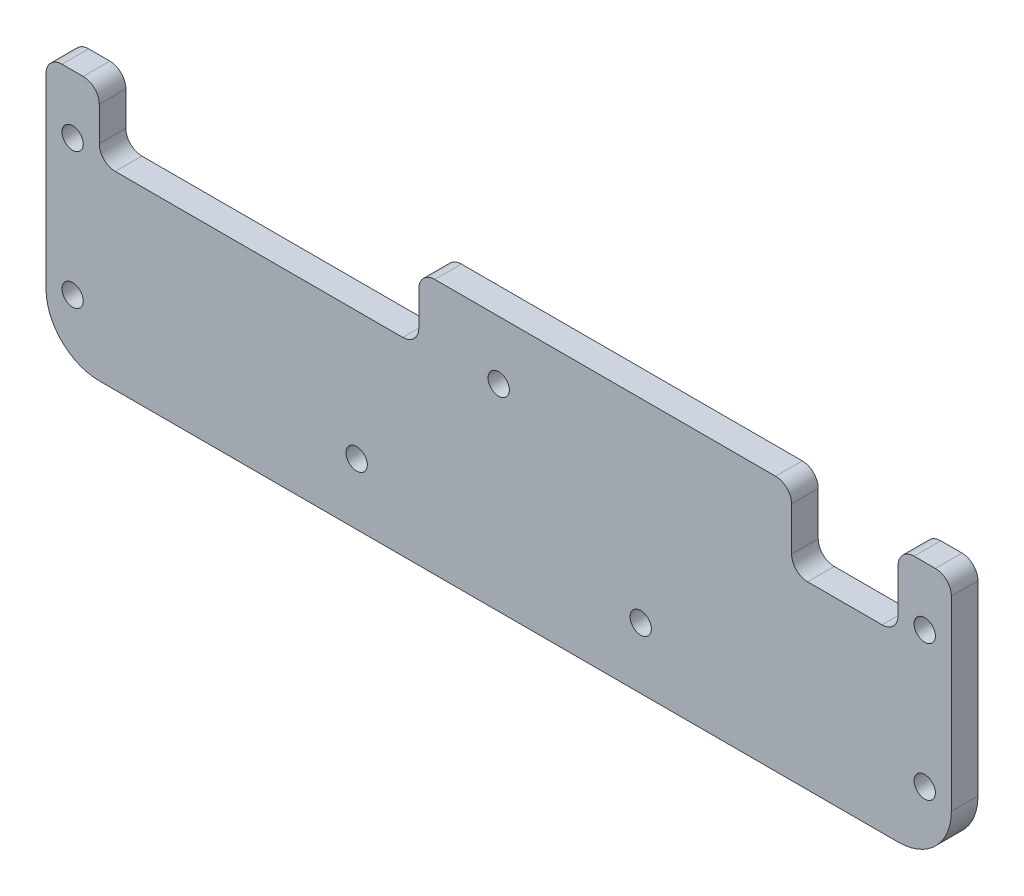
SolidWorks part; units mm, degrees
material "Thornel Mat VMA"
ref_plane "前视基准面" through (0, 0, 0) normal (0, 0, 1) x (1, 0, 0)
ref_plane "上视基准面" through (0, 0, 0) normal (0, 1, 0) x (1, 0, 0)
ref_plane "右视基准面" through (0, 0, 0) normal (1, 0, 0) x (0, 0, -1)
sketch "草图1" plane through (0, 0, 0) normal (0, 0, 1) x (1, 0, 0)
  line L0 (-85, 0) -> (85, 0)
  line L1 (-85, 0) -> (-85, -38)
  line L2 (-75, -48) -> (75, -48)
  line L3 (0, -2.75) -> (0, 2.75) construction
  line L4 (85, 0) -> (85, -38)
  arc A0 (-75, -48) -> (-85, -38) centre (-75, -38) cw
  circle A2 centre (-80, -11) radius 2
  circle A3 centre (0, -11) radius 2
  circle A4 centre (80, -11) radius 2
  circle A5 centre (-80, -36.5) radius 2
  circle A9 centre (80, -36.5) radius 2
  arc A10 (85, -38) -> (75, -48) centre (75, -38) cw
  circle A11 centre (-26.6667, -36.5) radius 2
  circle A12 centre (26.6667, -36.5) radius 2
  point P12 (0, -48)
  point P13 (0, 0)
  dimension "D3" = 10
  dimension "D7" = 4
  dimension "D8" = 4
  dimension "D9" = 4
  dimension "D10" = 36.5
  dimension "D15" = 10
  dimension "D12" = 4
  dimension "D17" = 4
  dimension "D19" = 4
  dimension "D1" = 85
  dimension "D2" = 48
  dimension "D4" = 80
  dimension "D5" = 80
  dimension "D6" = 11
  dimension "D13" = 5
  dimension "D14" = 5
  dimension "D16" = 5
  dimension "D20" = 26.6667
extrude "凸台-拉伸1" add sketch "草图1" along normal blind 5
sketch "草图2" plane through (0, 0, 0) normal (0, 0, 1) x (1, 0, 0)
  line L0 (-85, 0) -> (-85, -38) construction
  line L1 (-15, 12.1435) -> (-75, 12.1435)
  line L2 (-15, 12.1435) -> (-15, -12.4346)
  line L3 (-15, -12.4346) -> (-75, -12.4346)
  line L4 (-75, 12.1435) -> (-75, -12.4346)
  line L5 (75, 4.04) -> (55, 4.04)
  line L6 (75, 4.04) -> (75, -14.1694)
  line L7 (75, -14.1694) -> (55, -14.1694)
  line L8 (55, 4.04) -> (55, -14.1694)
  line L9 (85, -38) -> (85, 0) construction
  dimension "D1" = 10
  dimension "D2" = 20
  dimension "D3" = 10
  dimension "D4" = 60
extrude "切除-拉伸1" cut sketch "草图2" along normal blind 29
fillet "圆角1" radius 3 10 edges at (85, 0, 2.5) (-85, 0, 2.5) (-75, 0, 2.5) (-75, -12.4346, 2.5) (-15, -12.4346, 2.5) (-15, 0, 2.5) (55, -14.1694, 2.5) (55, 0, 2.5) (75, -14.1694, 2.5) (75, 0, 2.5)
